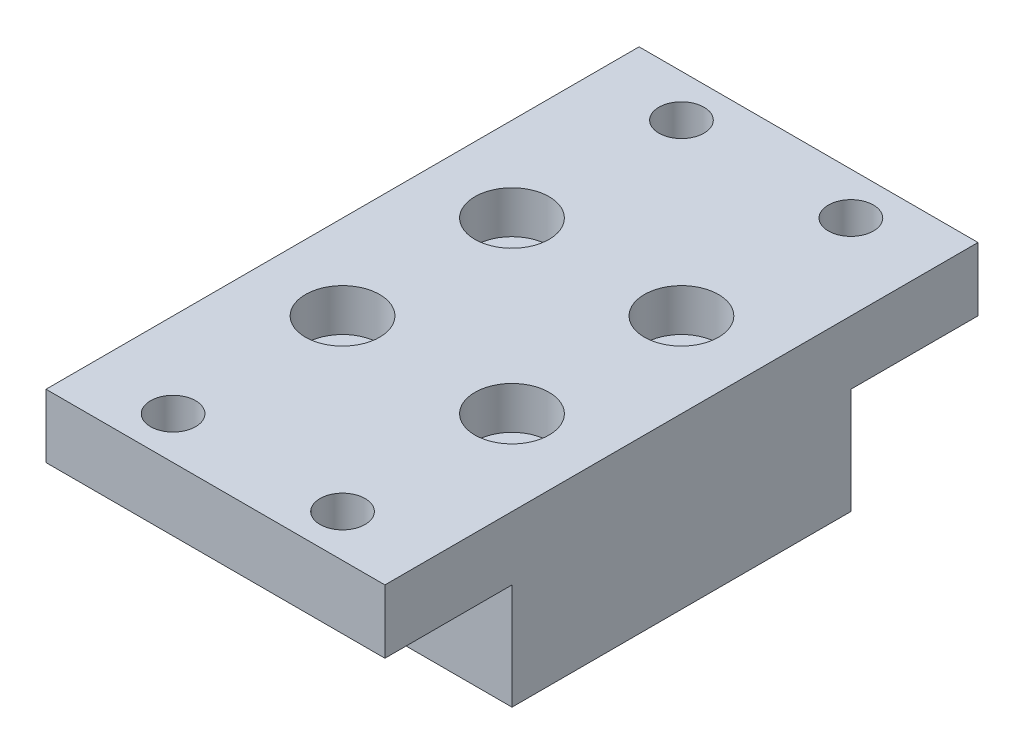
SolidWorks part; units mm, degrees
ref_plane "Front Plane" through (0, 0, 0) normal (0, 0, 1) x (1, 0, 0)
ref_plane "Top Plane" through (0, 0, 0) normal (0, 1, 0) x (1, 0, 0)
ref_plane "Right Plane" through (0, 0, 0) normal (1, 0, 0) x (0, 0, -1)
sketch "Sketch1" plane through (0, 0, 0) normal (0, 1, 0) x (1, 0, 0)
  line L1 (0, 0) -> (50.8, 0)
  line L2 (0, 0) -> (0, 50.8)
  line L3 (0, 50.8) -> (50.8, 50.8)
  line L4 (50.8, 0) -> (50.8, 50.8)
  dimension "D1" = 50.8
extrude "Boss-Extrude1" add sketch "Sketch1" along normal blind 25.4
sketch "Sketch7" plane through (0, 0, -50.8) normal (0, 0, -1) x (-1, 0, 0)
  line L0 (0, 25.4) -> (0, 0) construction
  line L1 (-50.8, 25.4) -> (0, 25.4)
  line L2 (-50.8, 25.4) -> (-50.8, 15.875)
  line L3 (-50.8, 15.875) -> (0, 15.875)
  line L4 (0, 25.4) -> (0, 15.875)
extrude "Boss-Extrude2" add sketch "Sketch7" along normal blind 19.05
sketch "Sketch11" plane through (0, 0, 0) normal (0, 0, 1) x (1, 0, 0)
  line L0 (50.8, 25.4) -> (50.8, 0) construction
  line L1 (0, 25.4) -> (50.8, 25.4)
  line L2 (0, 25.4) -> (0, 15.875)
  line L3 (0, 15.875) -> (50.8, 15.875)
  line L4 (50.8, 25.4) -> (50.8, 15.875)
extrude "Boss-Extrude3" add sketch "Sketch11" along normal blind 19.05
hole_wizard "1/4 Clearance Hole1" positions "Sketch6" profile "Sketch5" hole size "1/4" standard "Ansi Inch" end condition through all
sketch "Sketch6" plane through (0, 25.4, 0) normal (0, 1, 0) x (-1, 0, 0)
  line L0 (0, -69.85) -> (0, 19.05) construction
  line L2 (0, -69.85) -> (-50.8, -69.85) construction
  point P0 (-12.7, -63.5)
  dimension "D1" = 12.7
  dimension "D2" = 6.35
sketch "Sketch5" plane through (12.7, 25.4, -63.5) normal (1, 0, 0) x (0, 0, 1)
  line L0 (0, 0) -> (0, 25.4)
  line L1 (0, 25.4) -> (3.3782, 25.4)
  line L2 (3.3782, 25.4) -> (3.3782, 0)
  line L5 (3.3782, 0) -> (0, 0)
  line L11 (0, -6.35) -> (0, 107.95) construction
  dimension "Thru Hole Dia." = 6.7564
  dimension "Thru Hole Depth" = 25.4
hole_wizard "CBORE for 1/4 Socket Head Cap Screw1" positions "Sketch4" profile "Sketch3" counterbore size "1/4" standard "Ansi Inch" end condition through all
sketch "Sketch4" plane through (0, 25.4, 0) normal (0, 1, 0) x (-1, 0, 0)
  point P0 (-12.7, -12.7)
sketch "Sketch3" plane through (12.7, 25.4, -12.7) normal (1, 0, 0) x (0, 0, 1)
  line L0 (0, 0) -> (0, 25.4)
  line L1 (0, 25.4) -> (3.3782, 25.4)
  line L3 (3.3782, 25.4) -> (3.3782, 6.35)
  line L4 (3.3782, 6.35) -> (5.5562, 6.35)
  line L5 (5.5562, 6.35) -> (5.5563, 0)
  line L7 (5.5563, 0) -> (0, 0)
  line L11 (0, -6.35) -> (0, 107.95) construction
  dimension "Thru Hole Dia." = 6.7564
  dimension "Thru Hole Depth" = 25.4
  dimension "C'Bore Dia." = 11.1125
  dimension "C'Bore Depth" = 6.35
pattern_linear "LPattern1" count 4 spacing 25.4 along (0, 0, 1) count 2 spacing 25.4 along (1, 0, 0) of "1/4 Clearance Hole1"
pattern_linear "LPattern2" count 2 spacing 25.4 along (0, 0, -1) count 2 spacing 25.4 along (1, 0, 0) of "CBORE for 1/4 Socket Head Cap Screw1"
